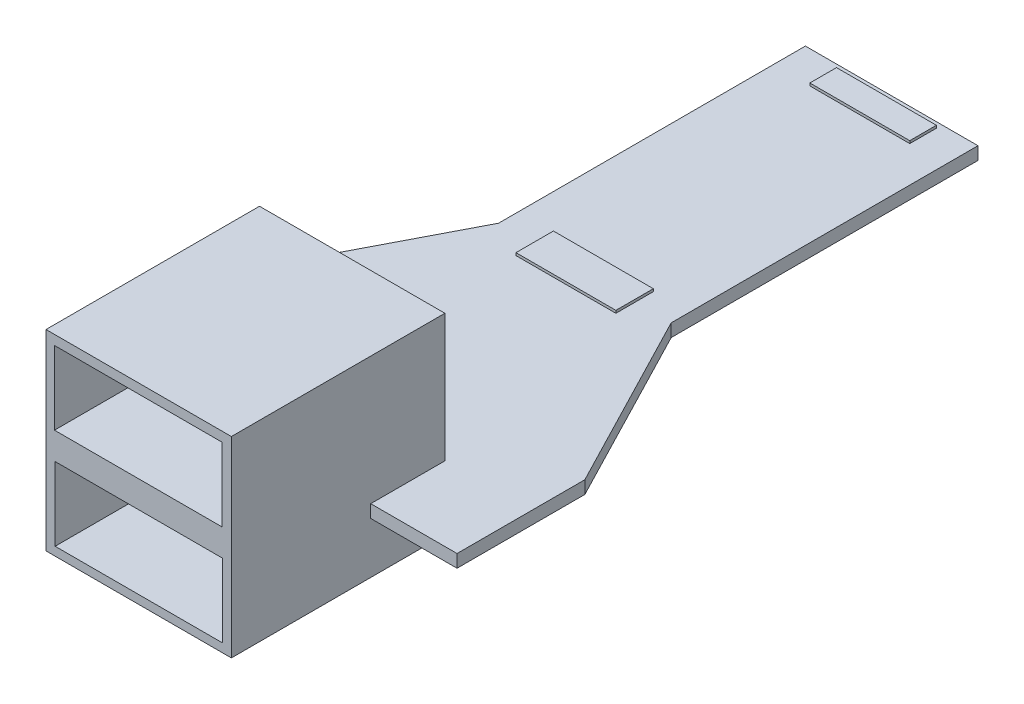
SolidWorks part; units mm, degrees
ref_plane "Front Plane" through (0, 0, 0) normal (0, 0, 1) x (1, 0, 0)
ref_plane "Top Plane" through (0, 0, 0) normal (0, 1, 0) x (1, 0, 0)
ref_plane "Right Plane" through (0, 0, 0) normal (1, 0, 0) x (0, 0, -1)
sketch "Sketch1" plane through (0, 0, 0) normal (0, 1, 0) x (1, 0, 0)
  line L0 (8.603, 15.7425) -> (15.853, 1.7425)
  line L1 (-12.147, 1.7425) -> (15.853, 1.7425)
  line L2 (-12.147, 1.7425) -> (-12.147, -8.2575)
  line L3 (-12.147, -8.2575) -> (15.853, -8.2575)
  line L4 (15.853, 1.7425) -> (15.853, -8.2575)
  line L5 (-4.897, 39.7425) -> (8.603, 39.7425)
  line L6 (-4.897, 39.7425) -> (-4.897, 15.7425)
  line L7 (-4.897, 15.7425) -> (8.603, 15.7425)
  line L8 (8.603, 39.7425) -> (8.603, 15.7425)
  line L9 (-4.897, 15.7425) -> (-12.147, 1.7425)
  dimension "D1" = 28
  dimension "D2" = 13.5
  dimension "D3" = 7.25
  dimension "D4" = 10
  dimension "D5" = 48
  dimension "D6" = 24
extrude "Boss-Extrude1" add sketch "Sketch1" along normal blind 1 contours L7 L9 L1 L0 | L4 L1 L2 L3 | L8 L5 L6 L7
ref_plane "Plane1" through (0, 11, 0) normal (0, 1, 0) x (1, 0, 0)
sketch "Sketch2" plane through (0, 11, 0) normal (0, 1, 0) x (1, 0, 0)
  line L0 (15.853, 1.7425) -> (15.853, -8.2575) construction
  line L1 (-5.397, -2.4575) -> (9.103, -2.4575)
  line L2 (-5.397, -2.4575) -> (-5.397, -19.1575)
  line L3 (-5.397, -19.1575) -> (9.103, -19.1575)
  line L4 (9.103, -2.4575) -> (9.103, -19.1575)
  line L6 (-12.147, -8.2575) -> (15.853, -8.2575) construction
  dimension "D1" = 14.5
  dimension "D2" = 6.75
  dimension "D3" = 16.7
  dimension "D4" = 5.8
extrude "Boss-Extrude2" add sketch "Sketch2" against normal blind 15
sketch "Sketch3" plane through (0, 0, 19.1575) normal (0, 0, 1) x (1, 0, 0)
  line L1 (-4.7334, 10.2508) -> (8.3666, 10.2508)
  line L2 (-4.7334, 10.2508) -> (-4.7334, 4.5108)
  line L3 (-4.7334, 4.5108) -> (8.3666, 4.5108)
  line L4 (8.3666, 10.2508) -> (8.3666, 4.5108)
  line L5 (-4.6829, 2.4128) -> (8.4171, 2.4128)
  line L6 (-4.6829, 2.4128) -> (-4.6829, -3.3272)
  line L7 (-4.6829, -3.3272) -> (8.4171, -3.3272)
  line L8 (8.4171, 2.4128) -> (8.4171, -3.3272)
  dimension "D1" = 13.1
  dimension "D2" = 13.1
  dimension "D3" = 5.74
  dimension "D4" = 5.74
extrude "Cut-Extrude1" cut sketch "Sketch3" against normal blind 10
sketch "Sketch4" plane through (0, 1, 0) normal (0, 1, 0) x (1, 0, 0)
  line L1 (-2.0217, 17.1581) -> (5.7929, 17.1581)
  line L2 (-2.0217, 17.1581) -> (-2.0217, 14.2276)
  line L3 (-2.0217, 14.2276) -> (5.7929, 14.2276)
  line L4 (5.7929, 17.1581) -> (5.7929, 14.2276)
  line L5 (-2.0217, 39.2995) -> (5.7929, 39.2995)
  line L6 (-2.0217, 39.2995) -> (-2.0217, 37.2156)
  line L7 (-2.0217, 37.2156) -> (5.7929, 37.2156)
  line L8 (5.7929, 39.2995) -> (5.7929, 37.2156)
extrude "Boss-Extrude3" add sketch "Sketch4" along normal blind 0.2
